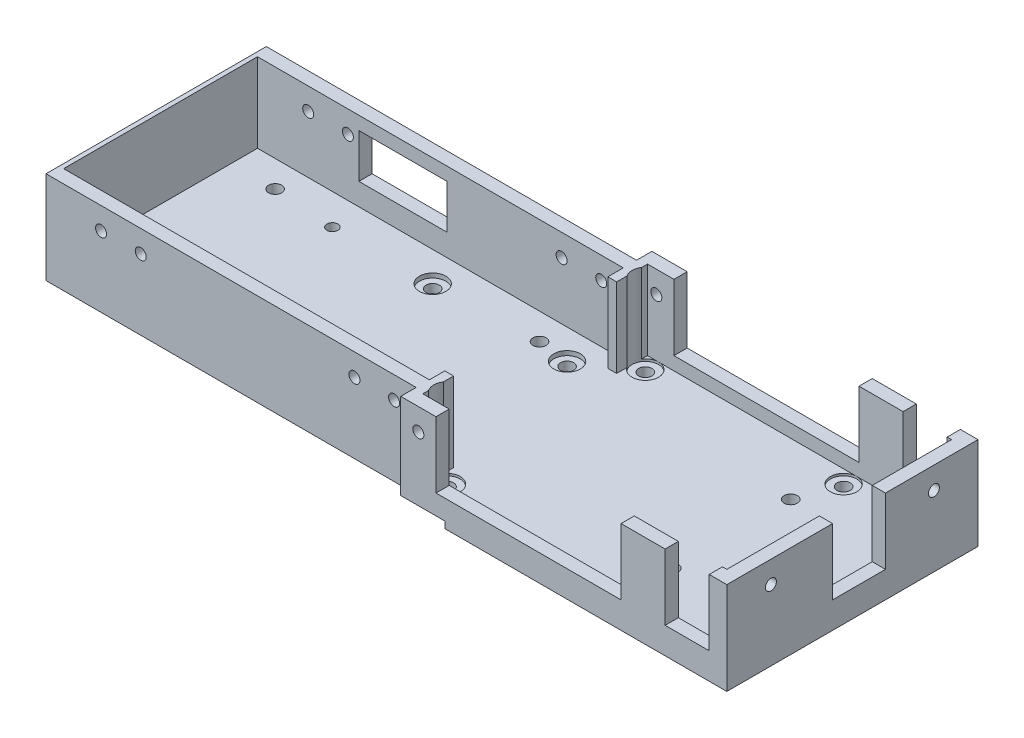
SolidWorks part; units mm, degrees
ref_plane "Front Plane" through (0, 0, 0) normal (0, 0, 1) x (1, 0, 0)
ref_plane "Top Plane" through (0, 0, 0) normal (0, 1, 0) x (1, 0, 0)
ref_plane "Right Plane" through (0, 0, 0) normal (1, 0, 0) x (0, 0, -1)
sketch "Sketch1" plane through (0, 0, 0) normal (0, 1, 0) x (1, 0, 0)
  line L1 (-122.6205, 21.9093) -> (35.3795, 21.9093)
  line L2 (-122.6205, 21.9093) -> (-122.6205, -28.0907)
  line L3 (-122.6205, -28.0907) -> (35.3795, -28.0907)
  line L4 (35.3795, 21.9093) -> (35.3795, -28.0907)
  dimension "D1" = 158
  dimension "D2" = 50
extrude "Boss-Extrude1" add sketch "Sketch1" along normal blind 3
sketch "Sketch2" plane through (0, 3, 0) normal (0, 1, 0) x (1, 0, 0)
  line L1 (35.3795, 21.9093) -> (-122.6205, 21.9093) construction
  line L2 (35.3795, -28.0907) -> (35.3795, 21.9093) construction
  line L3 (-122.6205, -28.0907) -> (35.3795, -28.0907) construction
  line L4 (-122.6205, 21.9093) -> (-122.6205, -28.0907) construction
  circle A0 centre (-75.1205, 12.1593) radius 1.5
  circle A1 centre (-75.1205, -18.3407) radius 1.5
  circle A2 centre (-44.6205, -18.3407) radius 1.5
  circle A3 centre (-44.6205, 12.1593) radius 1.5
  circle A6 centre (7.8795, -16.5907) radius 1.5
  circle A7 centre (7.8795, 10.4093) radius 1.5
  circle A8 centre (-111.6205, -19.0907) radius 1.5
  circle A9 centre (-111.6205, 12.9093) radius 1.5
  circle A13 centre (-97.6205, 11.9093) radius 1.25
  circle A14 centre (-97.6205, -18.0907) radius 1.25
  circle A15 centre (-51.6205, 12.9093) radius 1.5
  circle A16 centre (-51.6205, -19.0907) radius 1.5
  dimension "D1" = 3
  dimension "D2" = 3
  dimension "D3" = 3
  dimension "D4" = 3
  dimension "D13" = 27.5
  dimension "D14" = 27.5
  dimension "D19" = 3
  dimension "D20" = 3
  dimension "D25" = 3
  dimension "D26" = 3
  dimension "D37" = 2.5
  dimension "D38" = 2.5
  dimension "D43" = 3
  dimension "D44" = 3
  dimension "D15" = 11
  dimension "D5" = 52.5
  dimension "D6" = 9.75
  dimension "D7" = 52.5
  dimension "D8" = 30.5
  dimension "D9" = 30.5
  dimension "D10" = 30.5
  dimension "D11" = 9.75
  dimension "D12" = 30.5
  dimension "D16" = 11
  dimension "D17" = 22.5
  dimension "D18" = 22.5
  dimension "D23" = 27
  dimension "D24" = 11.5
  dimension "D27" = 32
  dimension "D28" = 9
  dimension "D39" = 30
  dimension "D42" = 10
  dimension "D45" = 60
  dimension "D46" = 60
  dimension "D47" = 32
  dimension "D48" = 9
extrude "Cut-Extrude1" cut sketch "Sketch2" against normal through all
sketch "Sketch4" plane through (0, 3, 0) normal (0, 1, 0) x (1, 0, 0)
  line L0 (35.3795, 21.9093) -> (-122.6205, 21.9093) construction
  line L1 (-38.6205, 25.4093) -> (35.3795, 25.4093)
  line L2 (-38.6205, 25.4093) -> (-38.6205, 21.9093)
  line L3 (-38.6205, 21.9093) -> (35.3795, 21.9093)
  line L4 (35.3795, 25.4093) -> (35.3795, 21.9093)
  line L5 (-38.6205, -28.0907) -> (35.3795, -28.0907)
  line L6 (-38.6205, -28.0907) -> (-38.6205, -31.5907)
  line L7 (-38.6205, -31.5907) -> (35.3795, -31.5907)
  line L8 (35.3795, -28.0907) -> (35.3795, -31.5907)
  line L9 (-122.6205, -28.0907) -> (35.3795, -28.0907) construction
  line L10 (35.3795, -28.0907) -> (35.3795, 21.9093) construction
  point P14 (35.3795, -29.8407)
  line M26 (-122.6205, -28.0907) -> (35.3795, -28.0907)
  dimension "D1" = 74
  dimension "D2" = 3.5
  dimension "D3" = 74
  dimension "D4" = 3.5
  dimension "D5" = 0
  dimension "D6" = 0
  dimension "D7" = 0
  dimension "D8" = 0
extrude "Boss-Extrude2" add sketch "Sketch4" against normal blind 3 contours L8 L6 L7 M26 | L2 L1 L4 L3
sketch "Sketch5" plane through (0, 3, 0) normal (0, 1, 0) x (1, 0, 0)
  line L0 (-38.6205, -31.5907) -> (35.3795, -31.5907) construction
  line L1 (-38.6205, 25.4093) -> (-38.6205, 21.9093) construction
  line L4 (-38.6205, -28.0907) -> (-38.6205, -31.5907) construction
  line L8 (-38.6205, 25.4093) -> (35.3795, 25.4093) construction
  circle A0 centre (-34.1205, 19.4093) radius 1.5
  circle A1 centre (-34.1205, -25.5907) radius 1.5
  circle A2 centre (10.8795, 19.4093) radius 1.5
  circle A3 centre (10.8795, -25.5907) radius 1.5
  dimension "D1" = 3
  dimension "D2" = 3
  dimension "D3" = 3
  dimension "D4" = 3
  dimension "D5" = 45
  dimension "D6" = 45
  dimension "D7" = 45
  dimension "D8" = 45
  dimension "D9" = 6
  dimension "D10" = 4.5
  dimension "D11" = 4.5
  dimension "D12" = 6
extrude "Cut-Extrude3" cut sketch "Sketch5" against normal through all
sketch "Sketch6" plane through (0, 3, 0) normal (0, 1, 0) x (1, 0, 0)
  line L0 (31.3795, 25.4093) -> (35.3795, 25.4093)
  line L5 (31.3795, 25.4093) -> (31.3795, 22.4093)
  line L6 (31.3795, 22.4093) -> (35.3795, 22.4093)
  line L7 (35.3795, 25.4093) -> (35.3795, 22.4093)
  line L8 (31.3795, -28.5907) -> (35.3795, -28.5907)
  line L9 (31.3795, -28.5907) -> (31.3795, -31.5907)
  line L10 (31.3795, -31.5907) -> (35.3795, -31.5907)
  line L11 (35.3795, -28.5907) -> (35.3795, -31.5907)
  line L12 (32.3795, 22.4093) -> (35.3795, 22.4093)
  line L13 (32.3795, 22.4093) -> (32.3795, 4.4093)
  line L14 (32.3795, 4.4093) -> (35.3795, 4.4093)
  line L15 (35.3795, 22.4093) -> (35.3795, 4.4093)
  line L16 (32.3795, -7.5907) -> (35.3795, -7.5907)
  line L17 (32.3795, -7.5907) -> (32.3795, -28.5907)
  line L18 (32.3795, -28.5907) -> (35.3795, -28.5907)
  line L19 (35.3795, -7.5907) -> (35.3795, -28.5907)
  line L20 (35.3795, -31.5907) -> (35.3795, 25.4093) construction
  line L21 (-38.6205, 25.4093) -> (35.3795, 25.4093) construction
  line L22 (11.3795, 25.4093) -> (21.3795, 25.4093)
  line L23 (-38.6205, -31.5907) -> (35.3795, -31.5907) construction
  line L24 (-38.6205, 25.4093) -> (-30.6205, 25.4093)
  line L25 (-38.6205, 25.4093) -> (-38.6205, 22.4093)
  line L26 (-38.6205, 22.4093) -> (-30.6205, 22.4093)
  line L27 (-30.6205, 25.4093) -> (-30.6205, 22.4093)
  line L28 (-38.6205, 22.4093) -> (-36.6205, 22.4093)
  line L29 (-38.6205, 22.4093) -> (-38.6205, 15.4093)
  line L30 (-38.6205, 15.4093) -> (-36.6205, 15.4093)
  line L31 (-36.6205, 22.4093) -> (-36.6205, 15.4093)
  line L32 (-38.6205, -21.5907) -> (-36.6205, -21.5907)
  line L33 (-38.6205, -21.5907) -> (-38.6205, -28.5907)
  line L34 (-38.6205, -28.5907) -> (-36.6205, -28.5907)
  line L35 (-36.6205, -21.5907) -> (-36.6205, -28.5907)
  line L36 (-38.6205, -28.5907) -> (-30.6205, -28.5907)
  line L37 (-38.6205, -28.5907) -> (-38.6205, -31.5907)
  line L38 (-38.6205, -31.5907) -> (-30.6205, -31.5907)
  line L39 (-30.6205, -28.5907) -> (-30.6205, -31.5907)
  line L40 (-38.6205, 25.4093) -> (-38.6205, 21.9093) construction
  line L41 (-38.6205, -28.0907) -> (-38.6205, -31.5907) construction
  line L42 (11.3795, 25.4093) -> (11.3795, 22.4093)
  line L43 (11.3795, 22.4093) -> (21.3795, 22.4093)
  line L44 (-38.6205, 21.9093) -> (-122.6205, 21.9093) construction
  line L45 (-122.6205, 21.9093) -> (-38.6205, 21.9093)
  line L46 (-122.6205, 21.9093) -> (-122.6205, 18.9093)
  line L47 (-122.6205, 18.9093) -> (-38.6205, 18.9093)
  line L48 (-38.6205, 21.9093) -> (-38.6205, 18.9093)
  line L49 (-122.6205, -28.0907) -> (-38.6205, -28.0907) construction
  line L50 (-122.6205, -25.0907) -> (-38.6205, -25.0907)
  line L51 (-122.6205, -25.0907) -> (-122.6205, -28.0907)
  line L52 (-122.6205, -28.0907) -> (-38.6205, -28.0907)
  line L53 (-38.6205, -25.0907) -> (-38.6205, -28.0907)
  line L54 (21.3795, 25.4093) -> (21.3795, 22.4093)
  line L55 (11.3795, -28.5907) -> (21.3795, -28.5907)
  line L56 (11.3795, -28.5907) -> (11.3795, -31.5907)
  line L57 (11.3795, -31.5907) -> (21.3795, -31.5907)
  line L58 (21.3795, -28.5907) -> (21.3795, -31.5907)
  line L63 (-122.6205, 21.9093) -> (-122.6205, -28.0907) construction
  point P24 (35.3795, 23.9093)
  line M45 (35.3795, -31.5907) -> (35.3795, 25.4093)
  line M46 (35.3795, 25.4093) -> (-38.6205, 25.4093)
  dimension "D13" = 18
  dimension "D20" = 3
  dimension "D1" = 0
  dimension "D2" = 0
  dimension "D3" = 0
  dimension "D4" = 3
  dimension "D5" = 4
  dimension "D6" = 0
  dimension "D7" = 0
  dimension "D8" = 0
  dimension "D9" = 3
  dimension "D10" = 4
  dimension "D11" = 0
  dimension "D12" = 0
  dimension "D14" = 3
  dimension "D15" = 3
  dimension "D16" = 8
  dimension "D17" = 3
  dimension "D18" = 0
  dimension "D19" = 0
  dimension "D21" = 8
  dimension "D22" = 0
  dimension "D23" = 0
  dimension "D24" = 2
  dimension "D25" = 2
  dimension "D26" = 7
  dimension "D27" = 7
  dimension "D28" = 0
  dimension "D29" = 0
  dimension "D30" = 0
  dimension "D31" = 0
  dimension "D32" = 0
  dimension "D33" = 3
  dimension "D34" = 0
  dimension "D35" = 0
  dimension "D36" = 0
  dimension "D37" = 3
  dimension "D38" = 0
  dimension "D39" = 0
  dimension "D40" = 0
  dimension "D41" = 10
  dimension "D42" = 10
  dimension "D43" = 3
  dimension "D44" = 0
  dimension "D45" = 10
  dimension "D46" = 10
  dimension "D47" = 3
  dimension "D48" = 21
extrude "Boss-Extrude3" add sketch "Sketch6" along normal blind 18 contours L5 L6 M45 M46 | L50 L53 L52 L51 | L45 L48 L47 L46 | L24 L27 L26 L25 | L36 L39 L38 L37 | L33 L34 L35 L32 | L31 L30 L29 L28 | L11 L10 L9 L8 | L19 L18 L17 L16 | L15 L14 L13 L12 | L55 L58 L57 L56 | L22 L54 L43 L42
sketch "Sketch8" plane through (0, 3, 0) normal (0, 1, 0) x (1, 0, 0)
  line L0 (21.3795, -28.5907) -> (31.3795, -28.5907)
  line L5 (21.3795, -28.5907) -> (21.3795, -31.5907)
  line L6 (21.3795, -31.5907) -> (31.3795, -31.5907)
  line L7 (31.3795, -28.5907) -> (31.3795, -31.5907)
  line L8 (31.3795, -28.5907) -> (31.3795, -31.5907) construction
  line L9 (21.3795, -31.5907) -> (31.3795, -31.5907) construction
  line L11 (21.3795, -28.5907) -> (21.3795, -31.5907) construction
  line L12 (21.3795, 25.4093) -> (31.3795, 25.4093)
  line L13 (21.3795, 25.4093) -> (21.3795, 23.4093)
  line L14 (21.3795, 23.4093) -> (31.3795, 23.4093)
  line L15 (31.3795, 25.4093) -> (31.3795, 23.4093)
  line L16 (21.3795, 25.4093) -> (31.3795, 25.4093) construction
  line L17 (21.3795, 25.4093) -> (21.3795, 22.4093) construction
  line L18 (31.3795, 25.4093) -> (31.3795, 22.4093) construction
  line L19 (-30.6205, 25.4093) -> (11.3795, 25.4093)
  line L20 (-30.6205, 25.4093) -> (-30.6205, 22.4093)
  line L21 (-30.6205, 22.4093) -> (11.3795, 22.4093)
  line L22 (11.3795, 25.4093) -> (11.3795, 22.4093)
  line L23 (-30.6205, 25.4093) -> (11.3795, 25.4093) construction
  line L24 (11.3795, 25.4093) -> (11.3795, 22.4093) construction
  line L25 (-30.6205, 25.4093) -> (-30.6205, 22.4093) construction
  line L26 (-30.6205, -28.5907) -> (11.3795, -28.5907)
  line L27 (-30.6205, -28.5907) -> (-30.6205, -31.5907)
  line L28 (-30.6205, -31.5907) -> (11.3795, -31.5907)
  line L29 (11.3795, -28.5907) -> (11.3795, -31.5907)
  line L30 (-30.6205, -31.5907) -> (11.3795, -31.5907) construction
  line L31 (-30.6205, -28.5907) -> (-30.6205, -31.5907) construction
  line L32 (11.3795, -28.5907) -> (11.3795, -31.5907) construction
  line L33 (32.3795, 4.4093) -> (35.3795, 4.4093)
  line L34 (32.3795, 4.4093) -> (32.3795, -7.5907)
  line L35 (32.3795, -7.5907) -> (35.3795, -7.5907)
  line L36 (35.3795, 4.4093) -> (35.3795, -7.5907)
  line L38 (35.3795, -7.5907) -> (35.3795, 4.4093) construction
  line L39 (32.3795, 4.4093) -> (35.3795, 4.4093) construction
  line L40 (32.3795, -7.5907) -> (35.3795, -7.5907) construction
  dimension "D1" = 3
  dimension "D2" = 0
  dimension "D3" = 0
  dimension "D4" = 0
  dimension "D5" = 0
  dimension "D6" = 0
  dimension "D7" = 0
  dimension "D8" = 0
  dimension "D9" = 3
  dimension "D10" = 0
  dimension "D11" = 0
  dimension "D12" = 0
  dimension "D13" = 3
  dimension "D14" = 0
  dimension "D15" = 0
  dimension "D16" = 3
  dimension "D17" = 0
  dimension "D18" = 0
  dimension "D19" = 0
extrude "Boss-Extrude4" add sketch "Sketch8" along normal blind 3
sketch "Sketch9" plane through (0, 0, -21.9093) normal (0, 0, -1) x (-1, 0, 0)
  line L0 (38.6205, 0) -> (122.6205, 0) construction
  line L1 (98.6205, 8) -> (78.6205, 8)
  line L2 (98.6205, 8) -> (98.6205, 18)
  line L3 (98.6205, 18) -> (78.6205, 18)
  line L4 (78.6205, 8) -> (78.6205, 18)
  line L6 (38.6205, 0) -> (38.6205, 21) construction
  dimension "D1" = 20
  dimension "D2" = 10
  dimension "D3" = 8
  dimension "D4" = 40
extrude "Cut-Extrude4" cut sketch "Sketch9" against normal up to next
sketch "Sketch10" plane through (35.3795, 0, 0) normal (1, 0, 0) x (0, 0, -1)
  line L0 (-7.5907, 21) -> (-31.5907, 21) construction
  line L1 (-31.5907, 0) -> (-31.5907, 21) construction
  line L2 (25.4093, 0) -> (25.4093, 21) construction
  line L3 (25.4093, 21) -> (4.4093, 21) construction
  circle A0 centre (-21.5907, 16) radius 1.25
  circle A1 centre (15.4093, 16) radius 1.25
  dimension "D1" = 2.5
  dimension "D2" = 2.5
  dimension "D3" = 5
  dimension "D4" = 10
  dimension "D5" = 10
  dimension "D6" = 5
extrude "Cut-Extrude5" cut sketch "Sketch10" against normal up to next
sketch "Sketch11" plane through (0, 0, -21.9093) normal (0, 0, -1) x (-1, 0, 0)
  line L0 (122.6205, 21) -> (38.6205, 21) construction
  line L1 (38.6205, 0) -> (38.6205, 21) construction
  line L3 (98.6205, 18) -> (98.6205, 8) construction
  circle A0 centre (43.6205, 16) radius 1.25
  circle A1 centre (110.1205, 16) radius 1.25
  circle A2 centre (52.6205, 16) radius 1.25
  circle A3 centre (101.1205, 16) radius 1.25
  point P14 (101.058, 14.7566)
  dimension "D1" = 2.5
  dimension "D2" = 2.5
  dimension "D7" = 2.5
  dimension "D10" = 2.5
  dimension "D3" = 5
  dimension "D4" = 5
  dimension "D5" = 5
  dimension "D6" = 9
  dimension "D8" = 5
  dimension "D9" = 14
  dimension "D11" = 2.5
  dimension "D12" = 5
extrude "Cut-Extrude6" cut sketch "Sketch11" against normal through all
sketch "Sketch12" plane through (0, 0, -25.4093) normal (0, 0, -1) x (-1, 0, 0)
  line L0 (38.6205, 21) -> (30.6205, 21) construction
  line L2 (38.6205, 0) -> (38.6205, 21) construction
  circle A0 centre (34.6205, 16) radius 1.25
  dimension "D1" = 2.5
  dimension "D2" = 5
  dimension "D3" = 4
extrude "Cut-Extrude7" cut sketch "Sketch12" against normal through all
sketch "Sketch13" plane through (0, 0, 0) normal (0, -1, 0) x (-1, 0, 0)
  line L0 (38.6205, -31.5907) -> (-35.3795, -31.5907) construction
  line L1 (38.6205, -31.5907) -> (28.6205, -31.5907)
  line L2 (38.6205, -31.5907) -> (38.6205, -30.0907)
  line L3 (38.6205, -30.0907) -> (28.6205, -30.0907)
  line L4 (28.6205, -31.5907) -> (28.6205, -30.0907)
  line L5 (38.6205, 25.4093) -> (28.6205, 25.4093)
  line L6 (38.6205, 25.4093) -> (38.6205, 23.9093)
  line L7 (38.6205, 23.9093) -> (28.6205, 23.9093)
  line L8 (28.6205, 25.4093) -> (28.6205, 23.9093)
  line L9 (38.6205, -28.0907) -> (38.6205, -31.5907) construction
  line L10 (38.6205, 25.4093) -> (-35.3795, 25.4093) construction
  line L11 (38.6205, 25.4093) -> (38.6205, 21.9093) construction
  point P14 (38.6205, 24.6593)
  dimension "D1" = 10
  dimension "D2" = 10
  dimension "D3" = 1.5
  dimension "D4" = 1.5
  dimension "D5" = 0
  dimension "D6" = 0
  dimension "D7" = 0
  dimension "D8" = 0
extrude "Cut-Extrude8" cut sketch "Sketch13" against normal blind 1.5
sketch "Sketch14" plane through (0, 3, 0) normal (0, 1, 0) x (1, 0, 0)
  circle A0 centre (10.8795, -25.5907) radius 3
  circle A1 centre (10.8795, -25.5907) radius 1.5 construction
  circle A2 centre (-34.1205, -25.5907) radius 3
  circle A3 centre (-34.1205, 19.4093) radius 3
  circle A4 centre (10.8795, 19.4093) radius 3
  circle A5 centre (-34.1205, -25.5907) radius 1.5 construction
  circle A6 centre (-34.1205, 19.4093) radius 1.5 construction
  circle A7 centre (10.8795, 19.4093) radius 1.5 construction
  dimension "D1" = 6
extrude "Cut-Extrude9" cut sketch "Sketch14" against normal blind 0.5 and the other way through all
sketch "Sketch15" plane through (0, 3, 0) normal (0, 1, 0) x (1, 0, 0)
  circle A0 centre (-75.1205, 12.1593) radius 3
  circle A1 centre (-75.1205, -18.3407) radius 3
  circle A2 centre (-44.6205, 12.1593) radius 3
  circle A3 centre (-44.6205, -18.3407) radius 3
  circle A4 centre (-75.1205, 12.1593) radius 1.5 construction
  circle A7 centre (-75.1205, -18.3407) radius 1.5 construction
  circle A8 centre (-44.6205, 12.1593) radius 1.5 construction
  circle A9 centre (-44.6205, -18.3407) radius 1.5 construction
  dimension "D1" = 6
  dimension "D2" = 6
  dimension "D3" = 6
  dimension "D4" = 6
extrude "Cut-Extrude10" cut sketch "Sketch15" against normal blind 1
sketch "Sketch17" plane through (0, 3, 0) normal (0, 1, 0) x (1, 0, 0)
  line L0 (-122.6205, 18.9093) -> (-38.6205, 18.9093) construction
  line L1 (-122.6205, 18.9093) -> (-121.6205, 18.9093)
  line L2 (-122.6205, 18.9093) -> (-122.6205, -25.0907)
  line L3 (-122.6205, -25.0907) -> (-121.6205, -25.0907)
  line L4 (-121.6205, 18.9093) -> (-121.6205, -25.0907)
  line L5 (-122.6205, 18.9093) -> (-122.6205, -25.0907) construction
  line L6 (-122.6205, -25.0907) -> (-38.6205, -25.0907) construction
  dimension "D1" = 1
  dimension "D2" = 0
  dimension "D3" = 0
  dimension "D4" = 0
extrude "Boss-Extrude5" add sketch "Sketch17" along normal blind 18
